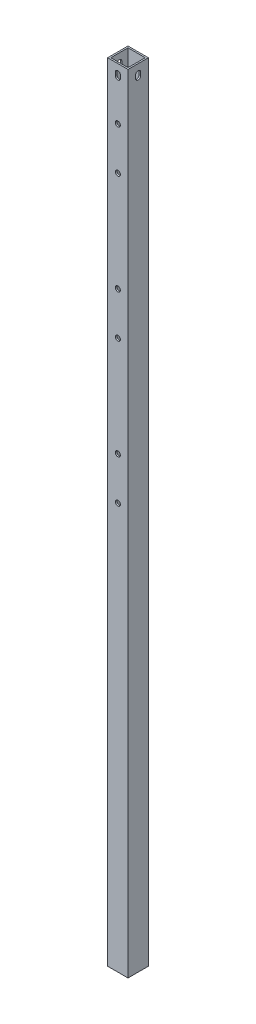
SolidWorks part; units mm, degrees
material "6061 Alloy"
ref_plane "Front Plane" through (0, 0, 0) normal (0, 0, 1) x (1, 0, 0)
ref_plane "Top Plane" through (0, 0, 0) normal (0, 1, 0) x (1, 0, 0)
ref_plane "Right Plane" through (0, 0, 0) normal (1, 0, 0) x (0, 0, -1)
sketch "Sketch1" plane through (0, 0, 0) normal (0, 1, 0) x (1, 0, 0)
  line L0 (-8.5, 8.5) -> (8.5, 8.5)
  line L1 (-10, 10) -> (10, 10)
  line L2 (-10, 10) -> (-10, -10)
  line L3 (-10, -10) -> (10, -10)
  line L4 (10, 10) -> (10, -10)
  line L5 (-10, 10) -> (10, -10) construction
  line L6 (-10, -10) -> (10, 10) construction
  line L7 (8.5, 8.5) -> (8.5, -8.5)
  line L8 (-8.5, -8.5) -> (8.5, -8.5)
  line L9 (-8.5, 8.5) -> (-8.5, -8.5)
  point P0 (0, 0)
  dimension "D1" = 20
  dimension "D2" = 1.5
extrude "Boss-Extrude1" add sketch "Sketch1" along normal blind 775.4
sketch "Sketch2" plane through (0, 0, 10) normal (0, 0, 1) x (1, 0, 0)
  line L0 (-10, 775.4) -> (10, 775.4) construction
  line L3 (-2.5, 766.9) -> (-2.5, 763.9)
  line L5 (2.5, 766.9) -> (2.5, 763.9)
  arc A0 (2.5, 766.9) -> (-2.5, 766.9) centre (0, 766.9) ccw
  arc A1 (-2.5, 763.9) -> (2.5, 763.9) centre (0, 763.9) ccw
  dimension "D1" = 5
  dimension "D2" = 8.5
  dimension "D3" = 3
extrude "Cut-Extrude1" cut sketch "Sketch2" against normal blind 5
sketch "Sketch3" plane through (0, 0, 10) normal (0, 0, 1) x (1, 0, 0)
  line L1 (0, 763.9) -> (0, 723.9)
  circle A2 centre (0, 723.9) radius 2.5
  circle A3 centre (0, 681.9) radius 2.5
  circle A4 centre (0, 583.1) radius 2.5
  circle A5 centre (0, 541.1) radius 2.5
  circle A6 centre (0, 442.3) radius 2.5
  circle A7 centre (0, 400.3) radius 2.5
  dimension "D2" = 5
  dimension "D3" = 5
  dimension "D4" = 42
  dimension "D5" = 140.8
  dimension "D6" = 42
  dimension "D7" = 281.6
  dimension "D8" = 42
  dimension "D9" = 5
  dimension "D10" = 5
  dimension "D11" = 5
  dimension "D12" = 5
  dimension "D1" = 40
extrude "Cut-Extrude8" cut sketch "Sketch3" against normal blind 5
sketch "Sketch10" plane through (-10, 0, 0) normal (-1, 0, 0) x (0, 0, 1)
  line L1 (-10, 775.4) -> (10, 775.4) construction
  line L4 (-2.5, 766.9) -> (-2.5, 763.9)
  line L6 (2.5, 766.9) -> (2.5, 763.9)
  arc A0 (2.5, 766.9) -> (-2.5, 766.9) centre (0, 766.9) ccw
  arc A1 (-2.5, 763.9) -> (2.5, 763.9) centre (0, 763.9) ccw
  dimension "D1" = 5
  dimension "D2" = 8.5
  dimension "D3" = 3
extrude "Cut-Extrude10" cut sketch "Sketch10" against normal blind 101
